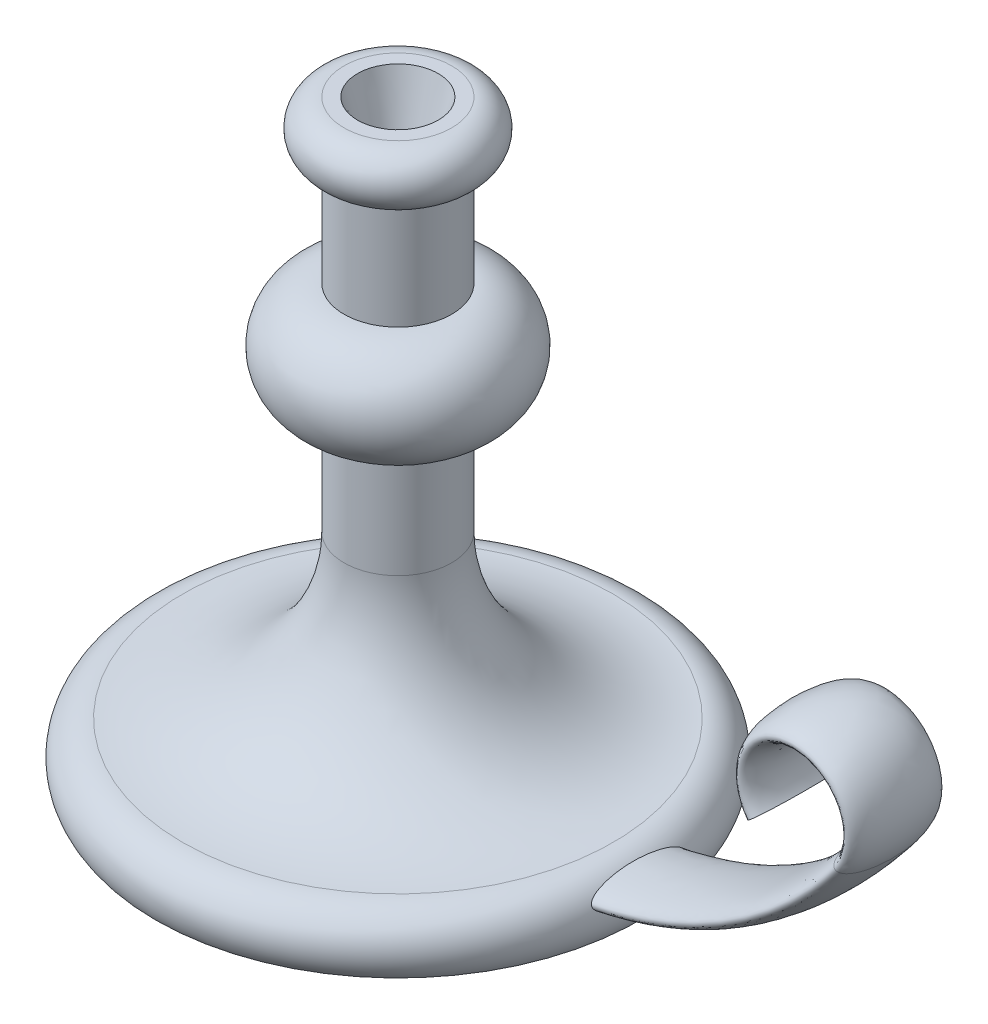
SolidWorks part; units mm, degrees
ref_plane "Front Plane" through (0, 0, 0) normal (0, 0, 1) x (1, 0, 0)
ref_plane "Top Plane" through (0, 0, 0) normal (0, 1, 0) x (1, 0, 0)
ref_plane "Right Plane" through (0, 0, 0) normal (1, 0, 0) x (0, 0, -1)
sketch "Sketch1" plane through (0, 0, 0) normal (0, 0, 1) x (1, 0, 0)
  line L0 (0, 0) -> (0, 220)
  line L1 (0, 220) -> (20, 220)
  line L2 (20, 200) -> (20, 160)
  line L3 (20, 120) -> (20, 80)
  line L4 (90, 0) -> (0, 0)
  arc A0 (20, 220) -> (20, 200) centre (20, 210) cw
  arc A1 (20, 160) -> (20, 120) centre (20, 140) cw
  arc A2 (20, 80) -> (80, 20) centre (80, 80) ccw
  arc A3 (80, 20) -> (90, 0) centre (80, 7.5) cw
  dimension "D3" = 10
  dimension "D5" = 20
  dimension "D7" = 60
  dimension "D8" = 12.5
  dimension "D1" = 220
  dimension "D2" = 20
  dimension "D4" = 40
  dimension "D6" = 80
  dimension "D9" = 90
revolve "Revolve1" add sketch "Sketch1" angle 360 about L0
sketch "Sketch2" plane through (0, 0, 0) normal (0, 0, 1) x (1, 0, 0)
  line L0 (0, 10) -> (60, 10)
  arc A0 (60, 10) -> (180, 70) centre (60, 160) ccw
  arc A1 (180, 70) -> (148, 70) centre (164, 82) ccw
  point P6 (0, 0)
  point P7 (0, 0)
  dimension "D3" = 150
  dimension "D4" = 20
  dimension "D1" = 10
  dimension "D2" = 60
  dimension "D5" = 60
sketch "Sketch3" plane through (0, 0, 0) normal (1, 0, 0) x (0, 0, -1)
  line L0 (0, 70) -> (0, 10) construction
  ellipse E0 centre (0, 10) end of major axis (-17.5, 10) minor radius 5
  point P1 (0, 0)
  point P7 (0, 0)
  point P11 (0, 0)
  point P12 (0, 0)
  point P13 (0, 0)
  dimension "D1" = 10
  dimension "D2" = 35
  dimension "D3" = 10
sweep "Sweep1" add profiles "Sketch3" path "Sketch2"
sketch "Sketch4" plane through (0, 220, 0) normal (0, 1, 0) x (1, 0, 0)
  circle A0 centre (0, 0) radius 15
  dimension "D1" = 30
extrude "Cut-Extrude1" cut sketch "Sketch4" against normal blind 25 draft 15
